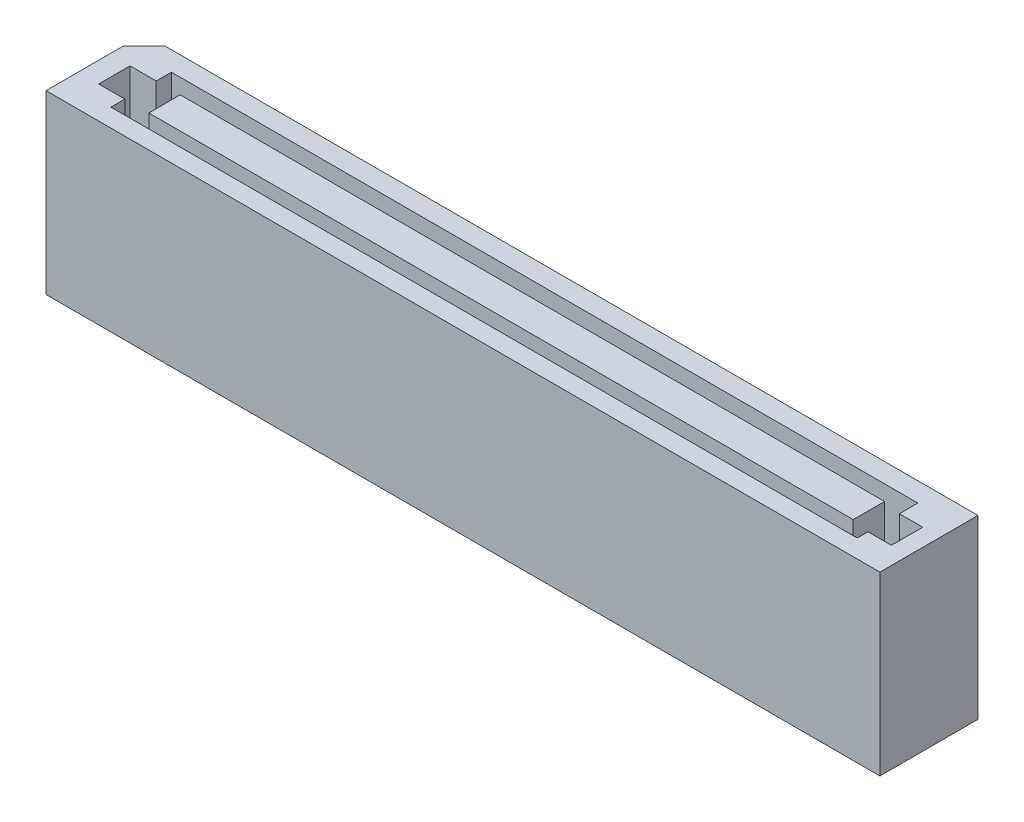
SolidWorks part; units mm, degrees
ref_plane "Front Plane" through (0, 0, 0) normal (0, 0, 1) x (1, 0, 0)
ref_plane "Top Plane" through (0, 0, 0) normal (0, 1, 0) x (1, 0, 0)
ref_plane "Right Plane" through (0, 0, 0) normal (1, 0, 0) x (0, 0, -1)
ref_plane "Plane1" through (0, -1.78, 0) normal (0, 1, 0) x (1, 0, 0)
ref_plane "center-of-slot" through (0, -0.89, 0) normal (0, 1, 0) x (1, 0, 0)
sketch "Sketch1" plane through (0, 0, 0) normal (0, 1, 0) x (1, 0, 0)
  line L13 (-20.189, 2.5) -> (21.25, 2.5)
  line L14 (-21.25, 1.439) -> (-21.25, -2.5)
  line L15 (-21.25, -2.5) -> (21.25, -2.5) construction
  line L16 (21.25, 2.5) -> (21.25, -2.5) construction
  line L20 (-21.25, 1.439) -> (-20.189, 2.5)
  line L33 (-21.25, -2.5) -> (20.19, -2.5)
  line L34 (20.19, -2.5) -> (21.25, -1.44) construction
  line L35 (21.25, -1.44) -> (21.25, 2.5)
  line L36 (20.19, -2.5) -> (21.25, -2.5)
  line L37 (21.25, -2.5) -> (21.25, -1.44)
  point P13 (-21.25, 2.5)
extrude "SV" add sketch "Sketch1" along normal blind 9
sketch "Sketch3" plane through (0, 9, 0) normal (0, 1, 0) x (1, 0, 0)
  line L60 (-20.2025, 0.7348) -> (-18.8675, 0.7348)
  line L61 (-20.2025, 1.5133) -> (20.3612, 1.5133) construction
  line L62 (-20.2025, 1.5133) -> (-20.2025, -1.5723) construction
  line L63 (-20.2025, -1.5723) -> (20.3612, -1.5723) construction
  line L64 (20.3612, 1.5133) -> (20.3612, -1.5723) construction
  line L65 (-18.8675, 0.7348) -> (-18.8675, 1.5133)
  line L66 (-18.8675, 1.5133) -> (19.1699, 1.5133)
  line L67 (19.1699, 1.5133) -> (19.1699, 0.5735)
  line L68 (19.1699, 0.5735) -> (20.3612, 0.5735)
  line L69 (20.3612, 0.5735) -> (20.3612, -1.0243)
  line L70 (20.3612, -1.0243) -> (19.1699, -1.0243)
  line L71 (19.1699, -1.0243) -> (19.1699, -1.5723)
  line L72 (19.1699, -1.5723) -> (-18.8675, -1.5723)
  line L73 (-18.8675, -1.5723) -> (-18.8675, -0.863)
  line L74 (-18.8675, -0.863) -> (-20.2025, -0.863)
  line L75 (-20.2025, -0.863) -> (-20.2025, 0.7348)
  line L76 (-17.6447, 0.7348) -> (18.253, 0.7348)
  line L77 (-17.6447, 0.7348) -> (-17.6447, -0.863)
  line L78 (-17.6447, -0.863) -> (18.253, -0.863)
  line L79 (18.253, 0.7348) -> (18.253, -0.863)
extrude "Cut-Extrude1" cut sketch "Sketch3" against normal blind 3.5
sketch "Sketch6" [suppressed] plane through (0, -1.78, 0) normal (0, 1, 0) x (1, 0, 0)
  line L0 (21.25, -1.4381) -> (21.25, -2.5)
  line L1 (-21.25, 2.5) -> (21.25, 2.5) construction
  line L2 (-21.25, 2.5) -> (-21.25, -2.5) construction
  line L3 (-21.25, -2.5) -> (21.25, -2.5) construction
  line L4 (21.25, 2.5) -> (21.25, -2.5) construction
  line L5 (21.25, -2.5) -> (20.1881, -2.5)
  line L6 (-20.19, 2.5) -> (-21.25, 1.44)
  line L21 (21.25, -1.4381) -> (21.25, 2.5)
  line L22 (20.1881, -2.5) -> (-21.25, -2.5)
  line L33 (-21.25, -2.5) -> (-21.25, 1.44)
  line L34 (-21.25, 1.44) -> (-20.19, 2.5) construction
  line L35 (-20.19, 2.5) -> (21.25, 2.5)
  point P0 (-21.25, 2.5)
extrude "SV2(a)" [suppressed] add sketch "Sketch6" against normal blind 3 separate body
sketch "Sketch7" [suppressed] plane through (0, -4.78, 0) normal (0, -1, 0) x (1, 0, 0)
  line L0 (-18.8675, -1.5133) -> (-18.8675, -0.7348)
  line L1 (-18.8675, -0.7348) -> (-20.2025, -0.7348)
  line L2 (-20.2025, -0.7348) -> (-20.2025, 0.863)
  line L3 (-20.2025, 0.863) -> (-18.8675, 0.863)
  line L4 (-18.8675, 0.863) -> (-18.8675, 1.5723)
  line L6 (-18.8675, 1.5723) -> (19.1699, 1.5723)
  line L7 (19.1699, 1.5723) -> (19.1699, 1.0243)
  line L8 (19.1699, 1.0243) -> (20.3612, 1.0243)
  line L9 (20.3612, 1.0243) -> (20.3612, -0.5735)
  line L10 (20.3612, -0.5735) -> (19.1699, -0.5735)
  line L11 (19.1699, -0.5735) -> (19.1699, -1.5133)
  line L12 (19.1699, -1.5133) -> (-18.8675, -1.5133)
  line L14 (-17.6447, -0.7348) -> (18.253, -0.7348)
  line L15 (-17.6447, -0.7348) -> (-17.6447, 0.863)
  line L16 (-17.6447, 0.863) -> (18.253, 0.863)
  line L17 (18.253, -0.7348) -> (18.253, 0.863)
extrude "SV2(b)" [suppressed] add sketch "Sketch7" along normal blind 3.5
